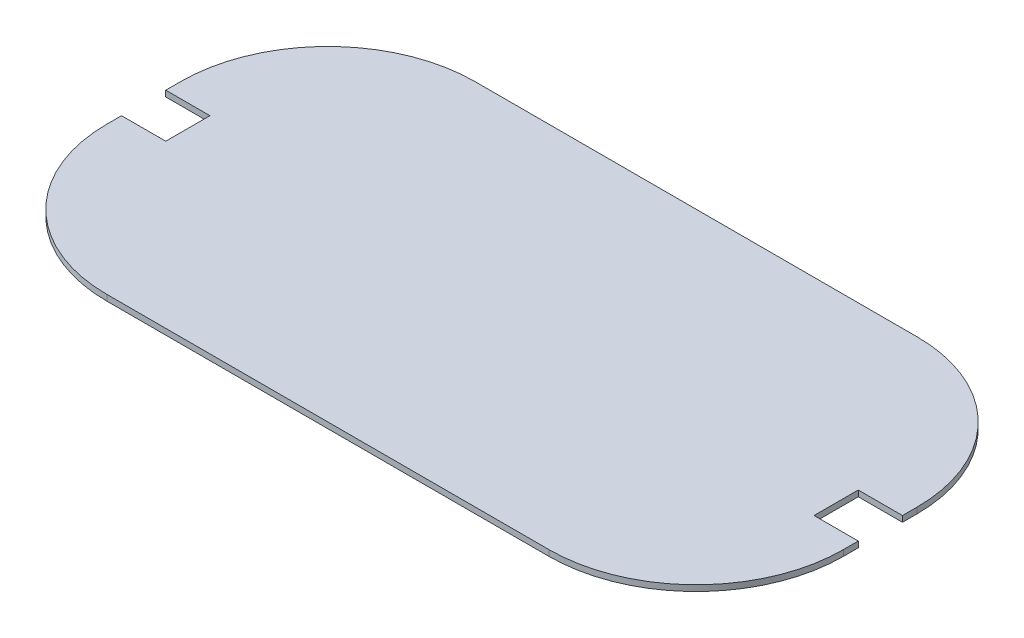
SolidWorks part; units mm, degrees
ref_plane "Front Plane" through (0, 0, 0) normal (0, 0, 1) x (1, 0, 0)
ref_plane "Top Plane" through (0, 0, 0) normal (0, 1, 0) x (1, 0, 0)
ref_plane "Right Plane" through (0, 0, 0) normal (1, 0, 0) x (0, 0, -1)
sketch "Sketch1" plane through (0, 0, 0) normal (0, 1, 0) x (1, 0, 0)
  line L1 (-250, -125) -> (250, -125)
  line L2 (-250, -125) -> (-250, 125)
  line L3 (-250, 125) -> (250, 125)
  line L4 (250, -125) -> (250, 125)
  line L5 (-250, -125) -> (250, 125) construction
  line L6 (-250, 125) -> (250, -125) construction
  point P0 (0, 0)
extrude "Boss-Extrude1" add sketch "Sketch1" along normal blind 4
fillet "Fillet1" radius 100 4 edges at (250, 2, 125) (250, 2, -125) (-250, 2, -125) (-250, 2, 125)
sketch "Sketch2" plane through (0, 0, 0) normal (0, -1, 0) x (-1, 0, 0)
  line L0 (250, 0) -> (250, -15)
  line L1 (250, 25) -> (250, -25) construction
  line L2 (250, -15) -> (220, -15)
  line L3 (220, -15) -> (220, 15)
  line L4 (220, 15) -> (250, 15)
  line L5 (250, 15) -> (250, 0)
  line L6 (-250, 0) -> (-250, -15)
  line L7 (-250, -25) -> (-250, 25) construction
  line L8 (-250, -15) -> (-220, -15)
  line L9 (-220, -15) -> (-220, 15)
  line L10 (-220, 15) -> (-250, 15)
  line L11 (-250, 15) -> (-250, 0)
extrude "Cut-Extrude1" cut sketch "Sketch2" against normal blind 10 contours L11 L6 L8 L9 L10 | L5 L0 L2 L3 L4
